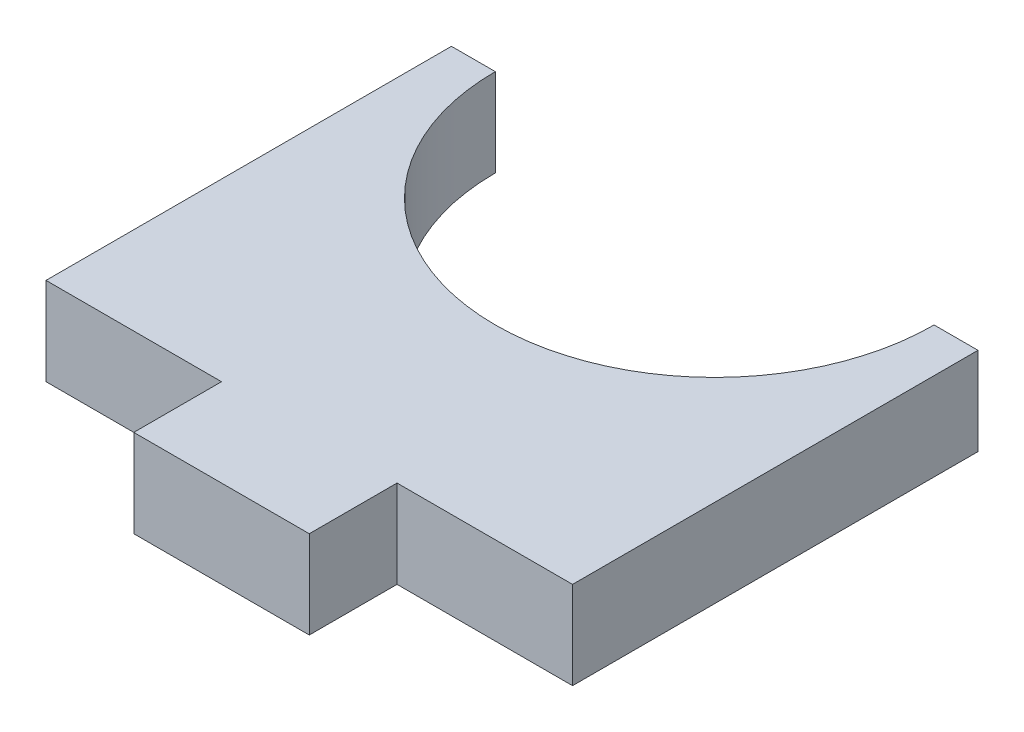
SolidWorks part; units mm, degrees
ref_plane "前视基准面" through (0, 0, 0) normal (0, 0, 1) x (1, 0, 0)
ref_plane "上视基准面" through (0, 0, 0) normal (0, 1, 0) x (1, 0, 0)
ref_plane "右视基准面" through (0, 0, 0) normal (1, 0, 0) x (0, 0, -1)
sketch "草图1" plane through (0, 0, 0) normal (0, 1, 0) x (1, 0, 0)
  line L1 (-15, -11.55) -> (15, -11.55)
  line L2 (-15, -11.55) -> (-15, 11.55)
  line L3 (-15, 11.55) -> (15, 11.55)
  line L4 (15, -11.55) -> (15, 11.55)
  line L5 (-15, -11.55) -> (15, 11.55) construction
  line L6 (-15, 11.55) -> (15, -11.55) construction
  line L7 (15, 11.55) -> (-15, 11.55)
  line L8 (15, 11.55) -> (15, 27.55)
  line L9 (15, 27.55) -> (-15, 27.55)
  line L10 (-15, 11.55) -> (-15, 27.55)
  circle A0 centre (0, 11.55) radius 12.5
  circle A1 centre (0, 11.55) radius 15
  point P0 (0, 0)
  dimension "D3" = 25
  dimension "D1" = 30
  dimension "D2" = 23.1
  dimension "D4" = 16
extrude "凸台-拉伸1" add sketch "草图1" along normal blind 5 contours L3 A1 A0 | L3 A1 A0 | A1 L2 L1 L4
sketch "草图2" plane through (0, 5, 0) normal (0, 1, 0) x (1, 0, 0)
  circle A0 centre (0, 11.55) radius 12.5
  circle A1 centre (0, 11.55) radius 8.5 construction
  circle A2 centre (-8.5, 11.55) radius 1.5
  circle A3 centre (8.5, 11.55) radius 1.5
  circle A4 centre (0, 11.55) radius 4
  dimension "D1" = 17
  dimension "D2" = 3
  dimension "D3" = 3
  dimension "D4" = 8
extrude "凸台-拉伸2" add sketch "草图2" against normal blind 5
sketch "草图3" plane through (0, 5, 0) normal (0, 1, 0) x (1, 0, 0)
  line L0 (-15, -11.55) -> (15, -11.55) construction
  line L1 (-5, -11.55) -> (5, -11.55)
  line L2 (-5, -11.55) -> (-5, -16.55)
  line L3 (-5, -16.55) -> (5, -16.55)
  line L4 (5, -11.55) -> (5, -16.55)
  line L5 (-15, -11.55) -> (-15, 11.55) construction
  line L6 (15, -11.55) -> (15, 11.55) construction
  dimension "D1" = 10
  dimension "D2" = 10
  dimension "D3" = 5
extrude "凸台-拉伸3" add sketch "草图3" against normal blind 5
sketch "草图4" plane through (0, 5, 0) normal (0, 1, 0) x (1, 0, 0)
  line L0 (-15, 11.55) -> (-12.5, 11.55)
  line L1 (-12.5, 11.55) -> (12.5, 11.55)
  line L2 (12.5, 11.55) -> (15, 11.55)
  circle A0 centre (0, 11.55) radius 12.5
  arc M1 (15, 11.55) -> (-15, 11.55) centre (0, 11.55) ccw
  circle M9 centre (0, 11.55) radius 4
  circle M10 centre (8.5, 11.55) radius 1.5
  circle M11 centre (-8.5, 11.55) radius 1.5
  dimension "D1" = 25
extrude "切除-拉伸1" cut sketch "草图4" against normal blind 10 contours A0 L2 L0 M1 | L1 A0 M11 M9 M10 | L1 A0 M10 M9 M11
